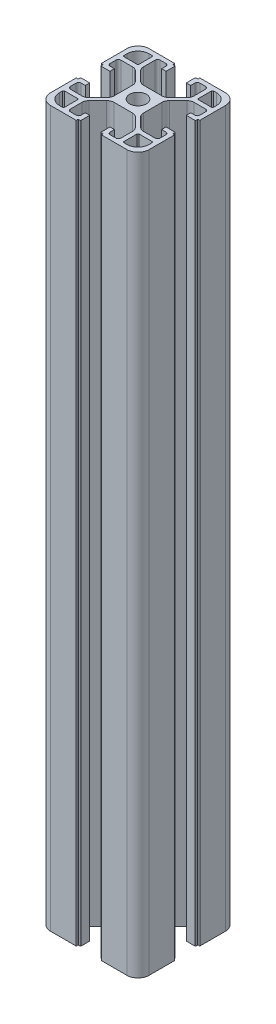
SolidWorks part; units mm, degrees
ref_plane "Front Plane" through (0, 0, 0) normal (0, 0, 1) x (1, 0, 0)
ref_plane "Top Plane" through (0, 0, 0) normal (0, 1, 0) x (1, 0, 0)
ref_plane "Right Plane" through (0, 0, 0) normal (1, 0, 0) x (0, 0, -1)
sketch "Sketch1" plane through (0, 0, 0) normal (0, 1, 0) x (1, 0, 0)
  line L0 (84.1702, 31.7204) -> (84.1702, 42.1204)
  line L1 (44.1702, 62.7204) -> (44.1702, 52.3204)
  line L2 (48.6702, 27.2204) -> (59.0702, 27.2204)
  line L3 (79.6702, 67.2204) -> (69.2702, 67.2204)
  line L4 (84.1702, 52.3204) -> (84.1702, 62.7204)
  line L6 (44.1702, 42.1204) -> (44.1702, 31.7204)
  line L7 (69.2702, 27.2204) -> (79.6702, 27.2204)
  line L10 (44.1702, 42.1204) -> (44.7702, 42.1204)
  line L11 (44.9702, 42.3204) -> (44.9702, 42.9204)
  line L12 (48.6702, 43.1204) -> (45.1702, 43.1204)
  line L13 (48.6702, 41.3204) -> (48.6702, 43.1204)
  line L14 (46.9702, 41.3204) -> (48.6702, 41.3204)
  line L15 (45.9702, 37.9704) -> (45.9702, 40.3204)
  line L16 (51.6169, 36.9704) -> (46.9702, 36.9704)
  line L17 (57.2915, 41.4024) -> (53.7382, 37.8491)
  line L18 (58.1702, 50.9171) -> (58.1702, 43.5237)
  line L19 (53.7382, 56.5917) -> (57.2915, 53.0384)
  line L20 (46.9702, 57.4704) -> (51.6169, 57.4704)
  line L21 (45.9702, 54.1204) -> (45.9702, 56.4704)
  line L22 (48.6702, 53.1204) -> (46.9702, 53.1204)
  line L23 (48.6702, 51.3204) -> (48.6702, 53.1204)
  line L24 (45.1702, 51.3204) -> (48.6702, 51.3204)
  line L25 (44.9702, 51.5204) -> (44.9702, 52.1204)
  line L26 (44.7702, 52.3204) -> (44.1702, 52.3204)
  line L28 (59.0702, 67.2204) -> (48.6702, 67.2204)
  line L29 (59.0702, 67.2204) -> (59.0702, 66.6204)
  line L30 (59.2702, 66.4204) -> (60.0702, 66.4204)
  line L31 (60.0702, 62.7204) -> (60.0702, 66.4204)
  line L32 (58.2702, 62.7204) -> (60.0702, 62.7204)
  line L33 (58.2702, 64.4204) -> (58.2702, 62.7204)
  line L34 (54.9202, 65.4204) -> (57.2702, 65.4204)
  line L35 (53.9202, 59.7737) -> (53.9202, 64.4204)
  line L36 (58.3522, 54.0991) -> (54.7989, 57.6524)
  line L37 (67.8669, 53.2204) -> (60.4735, 53.2204)
  line L38 (73.5415, 57.6524) -> (69.9882, 54.0991)
  line L39 (74.4202, 64.4204) -> (74.4202, 59.7737)
  line L40 (71.0702, 65.4204) -> (73.4202, 65.4204)
  line L41 (70.0702, 62.7204) -> (70.0702, 64.4204)
  line L42 (68.2702, 62.7204) -> (70.0702, 62.7204)
  line L43 (68.2702, 66.2204) -> (68.2702, 62.7204)
  line L44 (68.4702, 66.4204) -> (69.2702, 66.4204)
  line L45 (69.2702, 66.4204) -> (69.2702, 67.2204)
  line L48 (84.1702, 52.3204) -> (83.5702, 52.3204)
  line L49 (83.3702, 52.1204) -> (83.3702, 51.5204)
  line L50 (79.6702, 51.3204) -> (83.1702, 51.3204)
  line L51 (79.6702, 53.1204) -> (79.6702, 51.3204)
  line L52 (81.3702, 53.1204) -> (79.6702, 53.1204)
  line L53 (82.3702, 56.4704) -> (82.3702, 54.1204)
  line L54 (76.7235, 57.4704) -> (81.3702, 57.4704)
  line L55 (71.0489, 53.0384) -> (74.6022, 56.5917)
  line L56 (70.1702, 43.5237) -> (70.1702, 50.9171)
  line L57 (74.6022, 37.8491) -> (71.0489, 41.4024)
  line L58 (81.3702, 36.9704) -> (76.7235, 36.9704)
  line L59 (82.3702, 40.3204) -> (82.3702, 37.9704)
  line L60 (79.6702, 41.3204) -> (81.3702, 41.3204)
  line L61 (79.6702, 43.1204) -> (79.6702, 41.3204)
  line L62 (83.1702, 43.1204) -> (79.6702, 43.1204)
  line L63 (83.3702, 42.9204) -> (83.3702, 42.3204)
  line L64 (83.5702, 42.1204) -> (84.1702, 42.1204)
  line L67 (69.2702, 27.2204) -> (69.2702, 27.8204)
  line L68 (69.0702, 28.0204) -> (68.4702, 28.0204)
  line L69 (68.2702, 31.7204) -> (68.2702, 28.2204)
  line L70 (70.0702, 31.7204) -> (68.2702, 31.7204)
  line L71 (70.0702, 30.0204) -> (70.0702, 31.7204)
  line L72 (73.4202, 29.0204) -> (71.0702, 29.0204)
  line L73 (74.4202, 34.6671) -> (74.4202, 30.0204)
  line L74 (69.9882, 40.3417) -> (73.5415, 36.7884)
  line L75 (60.4735, 41.2204) -> (67.8669, 41.2204)
  line L76 (54.7989, 36.7884) -> (58.3522, 40.3417)
  line L77 (53.9202, 30.0204) -> (53.9202, 34.6671)
  line L78 (57.2702, 29.0204) -> (54.9202, 29.0204)
  line L79 (58.2702, 31.7204) -> (58.2702, 30.0204)
  line L80 (60.0702, 31.7204) -> (58.2702, 31.7204)
  line L81 (60.0702, 28.2204) -> (60.0702, 31.7204)
  line L82 (59.8702, 28.0204) -> (59.2702, 28.0204)
  line L83 (59.0702, 27.8204) -> (59.0702, 27.2204)
  line L84 (82.3702, 34.6704) -> (82.3702, 33.5204)
  line L85 (76.7202, 35.1704) -> (81.8702, 35.1704)
  line L86 (76.2202, 29.5204) -> (76.2202, 34.6704)
  line L87 (77.8702, 29.0204) -> (76.7202, 29.0204)
  line L88 (51.6202, 29.0204) -> (50.4702, 29.0204)
  line L89 (52.1202, 34.6704) -> (52.1202, 29.5204)
  line L90 (46.4702, 35.1704) -> (51.6202, 35.1704)
  line L91 (45.9702, 33.5204) -> (45.9702, 34.6704)
  line L92 (45.9702, 59.7704) -> (45.9702, 60.9204)
  line L93 (51.6202, 59.2704) -> (46.4702, 59.2704)
  line L94 (52.1202, 64.9204) -> (52.1202, 59.7704)
  line L95 (50.4702, 65.4204) -> (51.6202, 65.4204)
  line L96 (76.7202, 65.4204) -> (77.8702, 65.4204)
  line L97 (76.2202, 59.7704) -> (76.2202, 64.9204)
  line L98 (81.8702, 59.2704) -> (76.7202, 59.2704)
  line L99 (82.3702, 60.9204) -> (82.3702, 59.7704)
  arc A0 (60.7702, 47.2204) -> (67.5702, 47.2204) centre (64.1702, 47.2204) ccw
  arc A1 (44.1702, 31.7204) -> (48.6702, 27.2204) centre (48.6702, 31.7204) ccw
  arc A2 (44.7702, 42.1204) -> (44.9702, 42.3204) centre (44.7702, 42.3204) ccw
  arc A3 (45.1702, 43.1204) -> (44.9702, 42.9204) centre (45.1702, 42.9204) ccw
  arc A4 (46.9702, 41.3204) -> (45.9702, 40.3204) centre (46.9702, 40.3204) ccw
  arc A5 (45.9702, 37.9704) -> (46.9702, 36.9704) centre (46.9702, 37.9704) ccw
  arc A6 (51.6169, 36.9704) -> (53.7382, 37.8491) centre (51.6169, 39.9704) ccw
  arc A7 (57.2915, 41.4024) -> (58.1702, 43.5237) centre (55.1702, 43.5237) ccw
  arc A8 (58.1702, 50.9171) -> (57.2915, 53.0384) centre (55.1702, 50.9171) ccw
  arc A9 (53.7382, 56.5917) -> (51.6169, 57.4704) centre (51.6169, 54.4704) ccw
  arc A10 (46.9702, 57.4704) -> (45.9702, 56.4704) centre (46.9702, 56.4704) ccw
  arc A11 (45.9702, 54.1204) -> (46.9702, 53.1204) centre (46.9702, 54.1204) ccw
  arc A12 (44.9702, 51.5204) -> (45.1702, 51.3204) centre (45.1702, 51.5204) ccw
  arc A13 (44.9702, 52.1204) -> (44.7702, 52.3204) centre (44.7702, 52.1204) ccw
  arc A14 (48.6702, 67.2204) -> (44.1702, 62.7204) centre (48.6702, 62.7204) ccw
  arc A15 (59.0702, 66.6204) -> (59.2702, 66.4204) centre (59.2702, 66.6204) ccw
  arc A16 (58.2702, 64.4204) -> (57.2702, 65.4204) centre (57.2702, 64.4204) ccw
  arc A17 (54.9202, 65.4204) -> (53.9202, 64.4204) centre (54.9202, 64.4204) ccw
  arc A18 (53.9202, 59.7737) -> (54.7989, 57.6524) centre (56.9202, 59.7737) ccw
  arc A19 (58.3522, 54.0991) -> (60.4735, 53.2204) centre (60.4735, 56.2204) ccw
  arc A20 (67.8669, 53.2204) -> (69.9882, 54.0991) centre (67.8669, 56.2204) ccw
  arc A21 (73.5415, 57.6524) -> (74.4202, 59.7737) centre (71.4202, 59.7737) ccw
  arc A22 (74.4202, 64.4204) -> (73.4202, 65.4204) centre (73.4202, 64.4204) ccw
  arc A23 (71.0702, 65.4204) -> (70.0702, 64.4204) centre (71.0702, 64.4204) ccw
  arc A24 (68.4702, 66.4204) -> (68.2702, 66.2204) centre (68.4702, 66.2204) ccw
  arc A25 (84.1702, 62.7204) -> (79.6702, 67.2204) centre (79.6702, 62.7204) ccw
  arc A26 (83.5702, 52.3204) -> (83.3702, 52.1204) centre (83.5702, 52.1204) ccw
  arc A27 (83.1702, 51.3204) -> (83.3702, 51.5204) centre (83.1702, 51.5204) ccw
  arc A28 (81.3702, 53.1204) -> (82.3702, 54.1204) centre (81.3702, 54.1204) ccw
  arc A29 (82.3702, 56.4704) -> (81.3702, 57.4704) centre (81.3702, 56.4704) ccw
  arc A30 (76.7235, 57.4704) -> (74.6022, 56.5917) centre (76.7235, 54.4704) ccw
  arc A31 (71.0489, 53.0384) -> (70.1702, 50.9171) centre (73.1702, 50.9171) ccw
  arc A32 (70.1702, 43.5237) -> (71.0489, 41.4024) centre (73.1702, 43.5237) ccw
  arc A33 (74.6022, 37.8491) -> (76.7235, 36.9704) centre (76.7235, 39.9704) ccw
  arc A34 (81.3702, 36.9704) -> (82.3702, 37.9704) centre (81.3702, 37.9704) ccw
  arc A35 (82.3702, 40.3204) -> (81.3702, 41.3204) centre (81.3702, 40.3204) ccw
  arc A36 (83.3702, 42.9204) -> (83.1702, 43.1204) centre (83.1702, 42.9204) ccw
  arc A37 (83.3702, 42.3204) -> (83.5702, 42.1204) centre (83.5702, 42.3204) ccw
  arc A38 (79.6702, 27.2204) -> (84.1702, 31.7204) centre (79.6702, 31.7204) ccw
  arc A39 (69.2702, 27.8204) -> (69.0702, 28.0204) centre (69.0702, 27.8204) ccw
  arc A40 (68.2702, 28.2204) -> (68.4702, 28.0204) centre (68.4702, 28.2204) ccw
  arc A41 (70.0702, 30.0204) -> (71.0702, 29.0204) centre (71.0702, 30.0204) ccw
  arc A42 (73.4202, 29.0204) -> (74.4202, 30.0204) centre (73.4202, 30.0204) ccw
  arc A43 (74.4202, 34.6671) -> (73.5415, 36.7884) centre (71.4202, 34.6671) ccw
  arc A44 (69.9882, 40.3417) -> (67.8669, 41.2204) centre (67.8669, 38.2204) ccw
  arc A45 (60.4735, 41.2204) -> (58.3522, 40.3417) centre (60.4735, 38.2204) ccw
  arc A46 (54.7989, 36.7884) -> (53.9202, 34.6671) centre (56.9202, 34.6671) ccw
  arc A47 (53.9202, 30.0204) -> (54.9202, 29.0204) centre (54.9202, 30.0204) ccw
  arc A48 (57.2702, 29.0204) -> (58.2702, 30.0204) centre (57.2702, 30.0204) ccw
  arc A49 (59.8702, 28.0204) -> (60.0702, 28.2204) centre (59.8702, 28.2204) ccw
  arc A50 (59.2702, 28.0204) -> (59.0702, 27.8204) centre (59.2702, 27.8204) ccw
  arc A51 (82.3702, 34.6704) -> (81.8702, 35.1704) centre (81.8702, 34.6704) ccw
  arc A52 (76.7202, 35.1704) -> (76.2202, 34.6704) centre (76.7202, 34.6704) ccw
  arc A53 (76.2202, 29.5204) -> (76.7202, 29.0204) centre (76.7202, 29.5204) ccw
  arc A54 (77.8702, 29.0204) -> (82.3702, 33.5204) centre (77.8702, 33.5204) ccw
  arc A55 (51.6202, 29.0204) -> (52.1202, 29.5204) centre (51.6202, 29.5204) ccw
  arc A56 (52.1202, 34.6704) -> (51.6202, 35.1704) centre (51.6202, 34.6704) ccw
  arc A57 (46.4702, 35.1704) -> (45.9702, 34.6704) centre (46.4702, 34.6704) ccw
  arc A58 (45.9702, 33.5204) -> (50.4702, 29.0204) centre (50.4702, 33.5204) ccw
  arc A59 (45.9702, 59.7704) -> (46.4702, 59.2704) centre (46.4702, 59.7704) ccw
  arc A60 (51.6202, 59.2704) -> (52.1202, 59.7704) centre (51.6202, 59.7704) ccw
  arc A61 (52.1202, 64.9204) -> (51.6202, 65.4204) centre (51.6202, 64.9204) ccw
  arc A62 (50.4702, 65.4204) -> (45.9702, 60.9204) centre (50.4702, 60.9204) ccw
  arc A63 (76.7202, 65.4204) -> (76.2202, 64.9204) centre (76.7202, 64.9204) ccw
  arc A64 (76.2202, 59.7704) -> (76.7202, 59.2704) centre (76.7202, 59.7704) ccw
  arc A65 (81.8702, 59.2704) -> (82.3702, 59.7704) centre (81.8702, 59.7704) ccw
  arc A66 (82.3702, 60.9204) -> (77.8702, 65.4204) centre (77.8702, 60.9204) ccw
  arc A67 (67.5702, 47.2204) -> (60.7702, 47.2204) centre (64.1702, 47.2204) ccw
extrude "Boss-Extrude1" add sketch "Sketch1" along normal blind 290.4 from offset 0
